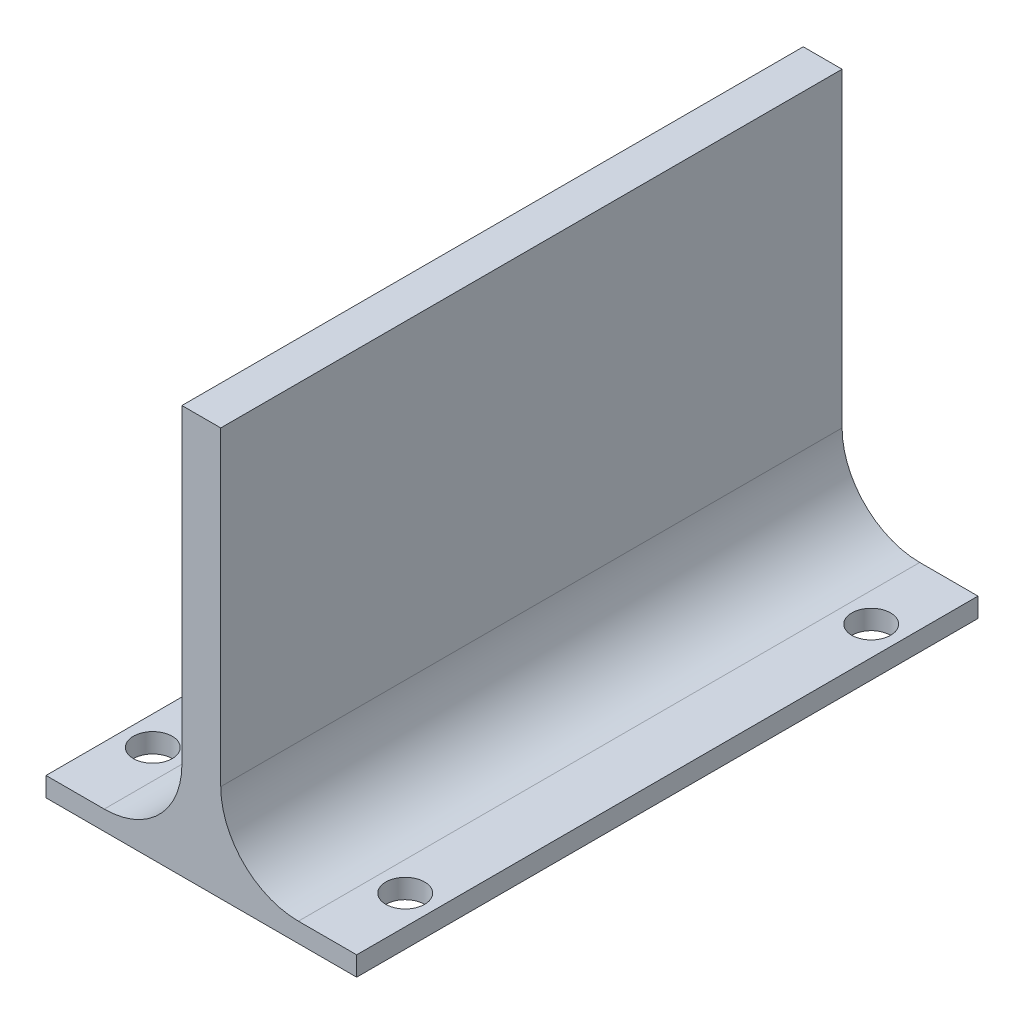
SolidWorks part; units mm, degrees
ref_plane "Front Plane" through (0, 0, 0) normal (0, 0, 1) x (1, 0, 0)
ref_plane "Top Plane" through (0, 0, 0) normal (0, 1, 0) x (1, 0, 0)
ref_plane "Right Plane" through (0, 0, 0) normal (1, 0, 0) x (0, 0, -1)
sketch "Sketch2" plane through (0, 0, 0) normal (0, 0, 1) x (1, 0, 0)
  line L0 (0, 0) -> (80, 0) construction
  line L1 (40, 0) -> (35, 0) construction
  line L2 (40, 0) -> (45, 0) construction
  line L3 (35, 0) -> (35, 100) construction
  line L4 (45, 0) -> (45, 100) construction
  line L6 (0, 0) -> (80, 0)
  line L7 (0, 0) -> (0, -5)
  line L8 (80, 0) -> (80, -5)
  line L9 (0, -5) -> (80, -5)
  line L10 (35, 0) -> (45, 0)
  line L11 (35, 0) -> (35, 100)
  line L12 (35, 100) -> (45, 100)
  line L13 (45, 0) -> (45, 100)
  point P3 (40, 0)
  dimension "D1" = 80
  dimension "D2" = 5
  dimension "D3" = 5
  dimension "D4" = 5
  dimension "D5" = 100
extrude "Boss-Extrude2" add sketch "Sketch2" along normal blind 160 contours L6 L13 L12 L11 | L7 L9 L8 L6
fillet "Fillet1" radius 20 2 edges at (45, 0, 80) (35, 0, 80)
sketch "Sketch3" plane through (0, 0, 0) normal (0, 1, 0) x (1, 0, 0)
  line L2 (72.5, 0) -> (72.5, -160) construction
  line L3 (65, 0) -> (80, 0) construction
  line L4 (65, -160) -> (80, -160) construction
  line L8 (7.5, -160) -> (7.5, 0) construction
  line L9 (0, -160) -> (15, -160) construction
  line L10 (-44, 0) -> (44, 0) construction
  line L11 (0, -57.75) -> (0, 57.75) construction
  circle A0 centre (72.5, -20) radius 5
  circle A3 centre (72.5, -140) radius 5
  circle A8 centre (7.5, -140) radius 5
  circle A9 centre (7.5, -20) radius 5
  dimension "D1" = 20
  dimension "D2" = 20
  dimension "D3" = 7.5
extrude "Cut-Extrude2" cut sketch "Sketch3" against normal blind 10
